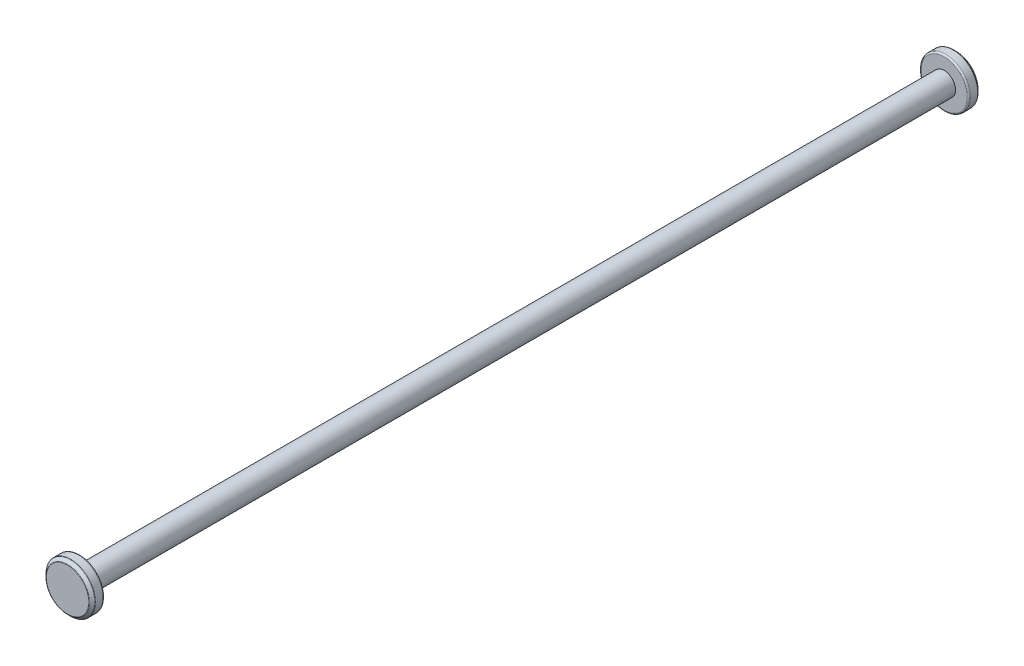
SolidWorks part; units mm, degrees
ref_plane "Front Plane" through (0, 0, 0) normal (0, 0, 1) x (1, 0, 0)
ref_plane "Top Plane" through (0, 0, 0) normal (0, 1, 0) x (1, 0, 0)
ref_plane "Right Plane" through (0, 0, 0) normal (1, 0, 0) x (0, 0, -1)
sketch "Sketch1" plane through (0, 0, 0) normal (0, 0, 1) x (1, 0, 0)
  circle A0 centre (0, 0) radius 1.85
  dimension "D1" = 3.7
extrude "Boss-Extrude1" add sketch "Sketch1" along normal mid plane 140.5
sketch "Sketch2" plane through (0, 0, -70.25) normal (0, 0, -1) x (-1, 0, 0)
  circle A2 centre (0, 0) radius 4
  dimension "D1" = 8
extrude "Boss-Extrude2" add sketch "Sketch2" along normal blind 2
chamfer "Chamfer1" distance 0.5 angle 45 1 edges at (-4, 0, -72.25)
fillet "Fillet2" radius 0.25 1 edges at (-4, 0, -70.25)
fillet "Fillet3" radius 0.125 2 edges at (-4, 0, -71.75) (-3.5, 0, -72.25)
mirror "Mirror2" about plane through (0, 0, 0) normal (0, 0, 1) of "Boss-Extrude2", "Chamfer1", "Fillet2", "Fillet3"
